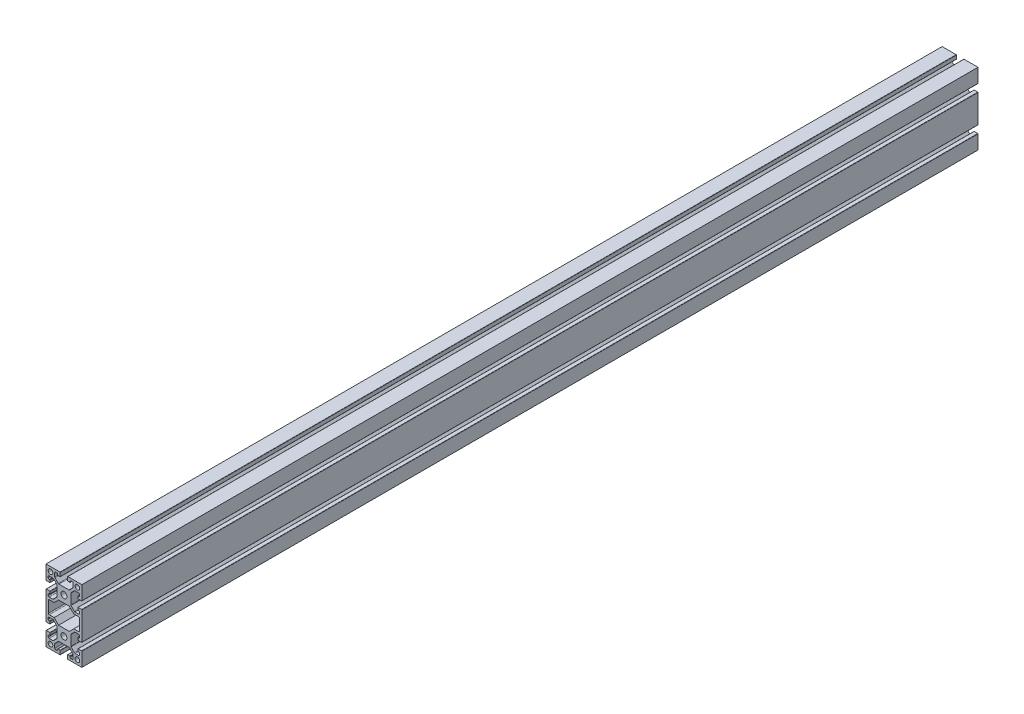
SolidWorks part; units mm, degrees
material "6063 T5"
ref_plane "Спереди" through (0, 0, 0) normal (0, 0, 1) x (1, 0, 0)
ref_plane "Сверху" through (0, 0, 0) normal (0, 1, 0) x (1, 0, 0)
ref_plane "Справа" through (0, 0, 0) normal (1, 0, 0) x (0, 0, -1)
sketch "Эскиз2" plane through (0, 0, 0) normal (0, 0, 1) x (1, 0, 0)
  line L0 (-20, 10.25) -> (-20, 20)
  line L1 (-20, 20) -> (-10.25, 20)
  line L2 (20, 20) -> (20, 10.25)
  line L3 (10.25, 20) -> (20, 20)
  line L4 (0, 0) -> (0, -40) construction
  line L5 (0, -20) -> (32.5246, -20) construction
  line L6 (10.25, -60) -> (20, -60)
  line L7 (20, -60) -> (20, -50.25)
  line L8 (20, -20) -> (10.25, -20) [skipped]
  line L9 (20, -10.25) -> (20, -20) [skipped]
  line L10 (-20, -20) -> (-20, -10.25) [skipped]
  line L11 (-10.25, -20) -> (-20, -20) [skipped]
  line L12 (-20, -60) -> (-10.25, -60)
  line L13 (-20, -50.25) -> (-20, -60)
  line L14 (-20, -10.25) -> (-20, -29.75)
  line L15 (20, -10.25) -> (20, -29.75)
  line L16 (-6, -7.8355) -> (6, -7.8355)
  line L17 (6, -7.8355) -> (10.9145, -12.75)
  line L18 (10.9145, -12.75) -> (16.4, -12.75)
  line L19 (17.4, -13.75) -> (17.4, -26.25)
  line L20 (-17.4, -13.75) -> (-17.4, -26.25)
  line L21 (-10.9145, -12.75) -> (-16.4, -12.75)
  line L22 (-6, -7.8355) -> (-10.9145, -12.75)
  line L23 (10.9145, -27.25) -> (16.4, -27.25)
  line L24 (6, -32.1645) -> (10.9145, -27.25)
  line L25 (-6, -32.1645) -> (6, -32.1645)
  line L26 (-6, -32.1645) -> (-10.9145, -27.25)
  line L27 (-10.9145, -27.25) -> (-16.4, -27.25)
  circle A0 centre (0, 0) radius 3.35
  circle A1 centre (-15, 15) radius 2.6
  circle A2 centre (15, 15) radius 2.6
  circle A5 centre (15, -15) radius 2.6 [skipped]
  circle A6 centre (-15, -15) radius 2.6 [skipped]
  circle A7 centre (15, -55) radius 2.6
  circle A8 centre (-15, -55) radius 2.6
  circle A9 centre (0, -40) radius 3.35
  arc A10 (16.4, -12.75) -> (17.4, -13.75) centre (16.4, -13.75) cw
  arc A11 (-16.4, -12.75) -> (-17.4, -13.75) centre (-16.4, -13.75) ccw
  arc A12 (16.4, -27.25) -> (17.4, -26.25) centre (16.4, -26.25) ccw
  arc A13 (-16.4, -27.25) -> (-17.4, -26.25) centre (-16.4, -26.25) cw
  point P14 (0, 0)
  point P22 (0, -40)
  point P23 (0, -40)
  point P27 (0, 0)
  point P57 (15, 15)
  point P60 (0, -7.8355)
  point P66 (17.4, -20)
  point P70 (-17.4, -20)
  line B0 (-20, 10.25) -> (-20, 4.4)
  line B1 (-19.7, 4.1) -> (-15.8, 4.1)
  line B2 (-15.5, 4.4) -> (-15.5, 6.6)
  line B3 (-15.8, 6.9) -> (-16.5, 6.9)
  line B4 (-17.5, 7.9) -> (-17.5, 9.25)
  line B5 (-16.5, 10.25) -> (-12.3642, 10.25)
  line B6 (-11.6571, 9.9571) -> (-7.9929, 6.2929)
  line B7 (-7.7, 5.5858) -> (-7.7, 0)
  line B8 (-7.7, 0) -> (-20, 0) construction
  line B9 (-11.6571, -9.9571) -> (-7.9929, -6.2929)
  line B10 (-16.5, -10.25) -> (-12.3642, -10.25)
  line B11 (-17.5, -7.9) -> (-17.5, -9.25)
  line B12 (-15.8, -6.9) -> (-16.5, -6.9)
  line B13 (-15.5, -4.4) -> (-15.5, -6.6)
  line B14 (-19.7, -4.1) -> (-15.8, -4.1)
  line B15 (-20, -10.25) -> (-20, -4.4)
  line B16 (-7.7, 0) -> (-7.7, -5.5858)
  arc B17 (-15.5, 6.6) -> (-15.8, 6.9) centre (-15.8, 6.6) ccw
  arc B18 (-15.8, 4.1) -> (-15.5, 4.4) centre (-15.8, 4.4) ccw
  arc B19 (-20, 4.4) -> (-19.7, 4.1) centre (-19.7, 4.4) ccw
  arc B20 (-7.9929, 6.2929) -> (-7.7, 5.5858) centre (-8.7, 5.5858) cw
  arc B21 (-12.3642, 10.25) -> (-11.6571, 9.9571) centre (-12.3642, 9.25) cw
  arc B22 (-17.5, 9.25) -> (-16.5, 10.25) centre (-16.5, 9.25) cw
  arc B23 (-16.5, 6.9) -> (-17.5, 7.9) centre (-16.5, 7.9) cw
  arc B24 (-16.5, -6.9) -> (-17.5, -7.9) centre (-16.5, -7.9) ccw
  arc B25 (-17.5, -9.25) -> (-16.5, -10.25) centre (-16.5, -9.25) ccw
  arc B26 (-12.3642, -10.25) -> (-11.6571, -9.9571) centre (-12.3642, -9.25) ccw
  arc B27 (-7.9929, -6.2929) -> (-7.7, -5.5858) centre (-8.7, -5.5858) ccw
  arc B28 (-20, -4.4) -> (-19.7, -4.1) centre (-19.7, -4.4) cw
  arc B29 (-15.8, -4.1) -> (-15.5, -4.4) centre (-15.8, -4.4) cw
  arc B30 (-15.5, -6.6) -> (-15.8, -6.9) centre (-15.8, -6.6) cw
  line B31 (10.25, 20) -> (4.4, 20)
  line B32 (4.1, 19.7) -> (4.1, 15.8)
  line B33 (4.4, 15.5) -> (6.6, 15.5)
  line B34 (6.9, 15.8) -> (6.9, 16.5)
  line B35 (7.9, 17.5) -> (9.25, 17.5)
  line B36 (10.25, 16.5) -> (10.25, 12.3642)
  line B37 (9.9571, 11.6571) -> (6.2929, 7.9929)
  line B38 (5.5858, 7.7) -> (0, 7.7)
  line B39 (0, 7.7) -> (0, 20) construction
  line B40 (-9.9571, 11.6571) -> (-6.2929, 7.9929)
  line B41 (-10.25, 16.5) -> (-10.25, 12.3642)
  line B42 (-7.9, 17.5) -> (-9.25, 17.5)
  line B43 (-6.9, 15.8) -> (-6.9, 16.5)
  line B44 (-4.4, 15.5) -> (-6.6, 15.5)
  line B45 (-4.1, 19.7) -> (-4.1, 15.8)
  line B46 (-10.25, 20) -> (-4.4, 20)
  line B47 (0, 7.7) -> (-5.5858, 7.7)
  arc B48 (6.6, 15.5) -> (6.9, 15.8) centre (6.6, 15.8) ccw
  arc B49 (4.1, 15.8) -> (4.4, 15.5) centre (4.4, 15.8) ccw
  arc B50 (4.4, 20) -> (4.1, 19.7) centre (4.4, 19.7) ccw
  arc B51 (6.2929, 7.9929) -> (5.5858, 7.7) centre (5.5858, 8.7) cw
  arc B52 (10.25, 12.3642) -> (9.9571, 11.6571) centre (9.25, 12.3642) cw
  arc B53 (9.25, 17.5) -> (10.25, 16.5) centre (9.25, 16.5) cw
  arc B54 (6.9, 16.5) -> (7.9, 17.5) centre (7.9, 16.5) cw
  arc B55 (-6.9, 16.5) -> (-7.9, 17.5) centre (-7.9, 16.5) ccw
  arc B56 (-9.25, 17.5) -> (-10.25, 16.5) centre (-9.25, 16.5) ccw
  arc B57 (-10.25, 12.3642) -> (-9.9571, 11.6571) centre (-9.25, 12.3642) ccw
  arc B58 (-6.2929, 7.9929) -> (-5.5858, 7.7) centre (-5.5858, 8.7) ccw
  arc B59 (-4.4, 20) -> (-4.1, 19.7) centre (-4.4, 19.7) cw
  arc B60 (-4.1, 15.8) -> (-4.4, 15.5) centre (-4.4, 15.8) cw
  arc B61 (-6.6, 15.5) -> (-6.9, 15.8) centre (-6.6, 15.8) cw
  line B62 (20, -10.25) -> (20, -4.4)
  line B63 (19.7, -4.1) -> (15.8, -4.1)
  line B64 (15.5, -4.4) -> (15.5, -6.6)
  line B65 (15.8, -6.9) -> (16.5, -6.9)
  line B66 (17.5, -7.9) -> (17.5, -9.25)
  line B67 (16.5, -10.25) -> (12.3642, -10.25)
  line B68 (11.6571, -9.9571) -> (7.9929, -6.2929)
  line B69 (7.7, -5.5858) -> (7.7, 0)
  line B70 (7.7, 0) -> (20, 0) construction
  line B71 (11.6571, 9.9571) -> (7.9929, 6.2929)
  line B72 (16.5, 10.25) -> (12.3642, 10.25)
  line B73 (17.5, 7.9) -> (17.5, 9.25)
  line B74 (15.8, 6.9) -> (16.5, 6.9)
  line B75 (15.5, 4.4) -> (15.5, 6.6)
  line B76 (19.7, 4.1) -> (15.8, 4.1)
  line B77 (20, 10.25) -> (20, 4.4)
  line B78 (7.7, 0) -> (7.7, 5.5858)
  arc B79 (15.5, -6.6) -> (15.8, -6.9) centre (15.8, -6.6) ccw
  arc B80 (15.8, -4.1) -> (15.5, -4.4) centre (15.8, -4.4) ccw
  arc B81 (20, -4.4) -> (19.7, -4.1) centre (19.7, -4.4) ccw
  arc B82 (7.9929, -6.2929) -> (7.7, -5.5858) centre (8.7, -5.5858) cw
  arc B83 (12.3642, -10.25) -> (11.6571, -9.9571) centre (12.3642, -9.25) cw
  arc B84 (17.5, -9.25) -> (16.5, -10.25) centre (16.5, -9.25) cw
  arc B85 (16.5, -6.9) -> (17.5, -7.9) centre (16.5, -7.9) cw
  arc B86 (16.5, 6.9) -> (17.5, 7.9) centre (16.5, 7.9) ccw
  arc B87 (17.5, 9.25) -> (16.5, 10.25) centre (16.5, 9.25) ccw
  arc B88 (12.3642, 10.25) -> (11.6571, 9.9571) centre (12.3642, 9.25) ccw
  arc B89 (7.9929, 6.2929) -> (7.7, 5.5858) centre (8.7, 5.5858) ccw
  arc B90 (20, 4.4) -> (19.7, 4.1) centre (19.7, 4.4) cw
  arc B91 (15.8, 4.1) -> (15.5, 4.4) centre (15.8, 4.4) cw
  arc B92 (15.5, 6.6) -> (15.8, 6.9) centre (15.8, 6.6) cw
  line B93 (-20, -50.25) -> (-20, -44.4)
  line B94 (-19.7, -44.1) -> (-15.8, -44.1)
  line B95 (-15.5, -44.4) -> (-15.5, -46.6)
  line B96 (-15.8, -46.9) -> (-16.5, -46.9)
  line B97 (-17.5, -47.9) -> (-17.5, -49.25)
  line B98 (-16.5, -50.25) -> (-12.3642, -50.25)
  line B99 (-11.6571, -49.9571) -> (-7.9929, -46.2929)
  line B100 (-7.7, -45.5858) -> (-7.7, -40)
  line B101 (-7.7, -40) -> (-20, -40) construction
  line B102 (-11.6571, -30.0429) -> (-7.9929, -33.7071)
  line B103 (-16.5, -29.75) -> (-12.3642, -29.75)
  line B104 (-17.5, -32.1) -> (-17.5, -30.75)
  line B105 (-15.8, -33.1) -> (-16.5, -33.1)
  line B106 (-15.5, -35.6) -> (-15.5, -33.4)
  line B107 (-19.7, -35.9) -> (-15.8, -35.9)
  line B108 (-20, -29.75) -> (-20, -35.6)
  line B109 (-7.7, -40) -> (-7.7, -34.4142)
  arc B110 (-15.5, -46.6) -> (-15.8, -46.9) centre (-15.8, -46.6) cw
  arc B111 (-15.8, -44.1) -> (-15.5, -44.4) centre (-15.8, -44.4) cw
  arc B112 (-20, -44.4) -> (-19.7, -44.1) centre (-19.7, -44.4) cw
  arc B113 (-7.9929, -46.2929) -> (-7.7, -45.5858) centre (-8.7, -45.5858) ccw
  arc B114 (-12.3642, -50.25) -> (-11.6571, -49.9571) centre (-12.3642, -49.25) ccw
  arc B115 (-17.5, -49.25) -> (-16.5, -50.25) centre (-16.5, -49.25) ccw
  arc B116 (-16.5, -46.9) -> (-17.5, -47.9) centre (-16.5, -47.9) ccw
  arc B117 (-16.5, -33.1) -> (-17.5, -32.1) centre (-16.5, -32.1) cw
  arc B118 (-17.5, -30.75) -> (-16.5, -29.75) centre (-16.5, -30.75) cw
  arc B119 (-12.3642, -29.75) -> (-11.6571, -30.0429) centre (-12.3642, -30.75) cw
  arc B120 (-7.9929, -33.7071) -> (-7.7, -34.4142) centre (-8.7, -34.4142) cw
  arc B121 (-20, -35.6) -> (-19.7, -35.9) centre (-19.7, -35.6) ccw
  arc B122 (-15.8, -35.9) -> (-15.5, -35.6) centre (-15.8, -35.6) ccw
  arc B123 (-15.5, -33.4) -> (-15.8, -33.1) centre (-15.8, -33.4) ccw
  line B124 (20, -29.75) -> (20, -35.6)
  line B125 (19.7, -35.9) -> (15.8, -35.9)
  line B126 (15.5, -35.6) -> (15.5, -33.4)
  line B127 (15.8, -33.1) -> (16.5, -33.1)
  line B128 (17.5, -32.1) -> (17.5, -30.75)
  line B129 (16.5, -29.75) -> (12.3642, -29.75)
  line B130 (11.6571, -30.0429) -> (7.9929, -33.7071)
  line B131 (7.7, -34.4142) -> (7.7, -40)
  line B132 (7.7, -40) -> (20, -40) construction
  line B133 (11.6571, -49.9571) -> (7.9929, -46.2929)
  line B134 (16.5, -50.25) -> (12.3642, -50.25)
  line B135 (17.5, -47.9) -> (17.5, -49.25)
  line B136 (15.8, -46.9) -> (16.5, -46.9)
  line B137 (15.5, -44.4) -> (15.5, -46.6)
  line B138 (19.7, -44.1) -> (15.8, -44.1)
  line B139 (20, -50.25) -> (20, -44.4)
  line B140 (7.7, -40) -> (7.7, -45.5858)
  arc B141 (15.5, -33.4) -> (15.8, -33.1) centre (15.8, -33.4) cw
  arc B142 (15.8, -35.9) -> (15.5, -35.6) centre (15.8, -35.6) cw
  arc B143 (20, -35.6) -> (19.7, -35.9) centre (19.7, -35.6) cw
  arc B144 (7.9929, -33.7071) -> (7.7, -34.4142) centre (8.7, -34.4142) ccw
  arc B145 (12.3642, -29.75) -> (11.6571, -30.0429) centre (12.3642, -30.75) ccw
  arc B146 (17.5, -30.75) -> (16.5, -29.75) centre (16.5, -30.75) ccw
  arc B147 (16.5, -33.1) -> (17.5, -32.1) centre (16.5, -32.1) ccw
  arc B148 (16.5, -46.9) -> (17.5, -47.9) centre (16.5, -47.9) cw
  arc B149 (17.5, -49.25) -> (16.5, -50.25) centre (16.5, -49.25) cw
  arc B150 (12.3642, -50.25) -> (11.6571, -49.9571) centre (12.3642, -49.25) cw
  arc B151 (7.9929, -46.2929) -> (7.7, -45.5858) centre (8.7, -45.5858) cw
  arc B152 (20, -44.4) -> (19.7, -44.1) centre (19.7, -44.4) ccw
  arc B153 (15.8, -44.1) -> (15.5, -44.4) centre (15.8, -44.4) ccw
  arc B154 (15.5, -46.6) -> (15.8, -46.9) centre (15.8, -46.6) ccw
  line B155 (10.25, -60) -> (4.4, -60)
  line B156 (4.1, -59.7) -> (4.1, -55.8)
  line B157 (4.4, -55.5) -> (6.6, -55.5)
  line B158 (6.9, -55.8) -> (6.9, -56.5)
  line B159 (7.9, -57.5) -> (9.25, -57.5)
  line B160 (10.25, -56.5) -> (10.25, -52.3642)
  line B161 (9.9571, -51.6571) -> (6.2929, -47.9929)
  line B162 (5.5858, -47.7) -> (0, -47.7)
  line B163 (0, -47.7) -> (0, -60) construction
  line B164 (-9.9571, -51.6571) -> (-6.2929, -47.9929)
  line B165 (-10.25, -56.5) -> (-10.25, -52.3642)
  line B166 (-7.9, -57.5) -> (-9.25, -57.5)
  line B167 (-6.9, -55.8) -> (-6.9, -56.5)
  line B168 (-4.4, -55.5) -> (-6.6, -55.5)
  line B169 (-4.1, -59.7) -> (-4.1, -55.8)
  line B170 (-10.25, -60) -> (-4.4, -60)
  line B171 (0, -47.7) -> (-5.5858, -47.7)
  arc B172 (6.6, -55.5) -> (6.9, -55.8) centre (6.6, -55.8) cw
  arc B173 (4.1, -55.8) -> (4.4, -55.5) centre (4.4, -55.8) cw
  arc B174 (4.4, -60) -> (4.1, -59.7) centre (4.4, -59.7) cw
  arc B175 (6.2929, -47.9929) -> (5.5858, -47.7) centre (5.5858, -48.7) ccw
  arc B176 (10.25, -52.3642) -> (9.9571, -51.6571) centre (9.25, -52.3642) ccw
  arc B177 (9.25, -57.5) -> (10.25, -56.5) centre (9.25, -56.5) ccw
  arc B178 (6.9, -56.5) -> (7.9, -57.5) centre (7.9, -56.5) ccw
  arc B179 (-6.9, -56.5) -> (-7.9, -57.5) centre (-7.9, -56.5) cw
  arc B180 (-9.25, -57.5) -> (-10.25, -56.5) centre (-9.25, -56.5) cw
  arc B181 (-10.25, -52.3642) -> (-9.9571, -51.6571) centre (-9.25, -52.3642) cw
  arc B182 (-6.2929, -47.9929) -> (-5.5858, -47.7) centre (-5.5858, -48.7) cw
  arc B183 (-4.4, -60) -> (-4.1, -59.7) centre (-4.4, -59.7) ccw
  arc B184 (-4.1, -55.8) -> (-4.4, -55.5) centre (-4.4, -55.8) ccw
  arc B185 (-6.6, -55.5) -> (-6.9, -55.8) centre (-6.6, -55.8) ccw
  dimension "D1" = 6.7
  dimension "D3" = 5.2
  dimension "D4" = 15
  dimension "D5" = 15
  dimension "D13" = 1
  dimension "D2" = 20
  dimension "D7" = 4
  dimension "D8" = 40
  dimension "D9" = 2.6
  dimension "D10" = 2.5
  dimension "D11" = 2.5
  dimension "D12" = 6
  dimension "D6" = 4
sketch_block_instance "8B(20,5PL_cut)-4"
sketch_block "8B(20,5PL_cut)" parameters "D7"=0.3, "D8"=1, "D12"=0.3, "D5"=0.3, "D1"=12.3, "D2"=4.5, "D3"=8.2, "D4"=20.5, "D6"=135, "D9"=1, "D10"=2.8, "D11"=2, "D13"=1.2, "D14"=11.8
sketch_block_instance "8B(20,5PL_cut)-6"
sketch_block_instance "8B(20,5PL_cut)-7"
sketch_block_instance "8B(20,5PL_cut)-9"
sketch_block_instance "8B(20,5PL_cut)-10"
sketch_block_instance "8B(20,5PL_cut)-11"
sketch_block_instance "8B(20,5PL_cut)-12"
extrude "Бобышка-Вытянуть1" add sketch "Эскиз2" along normal blind 1000
